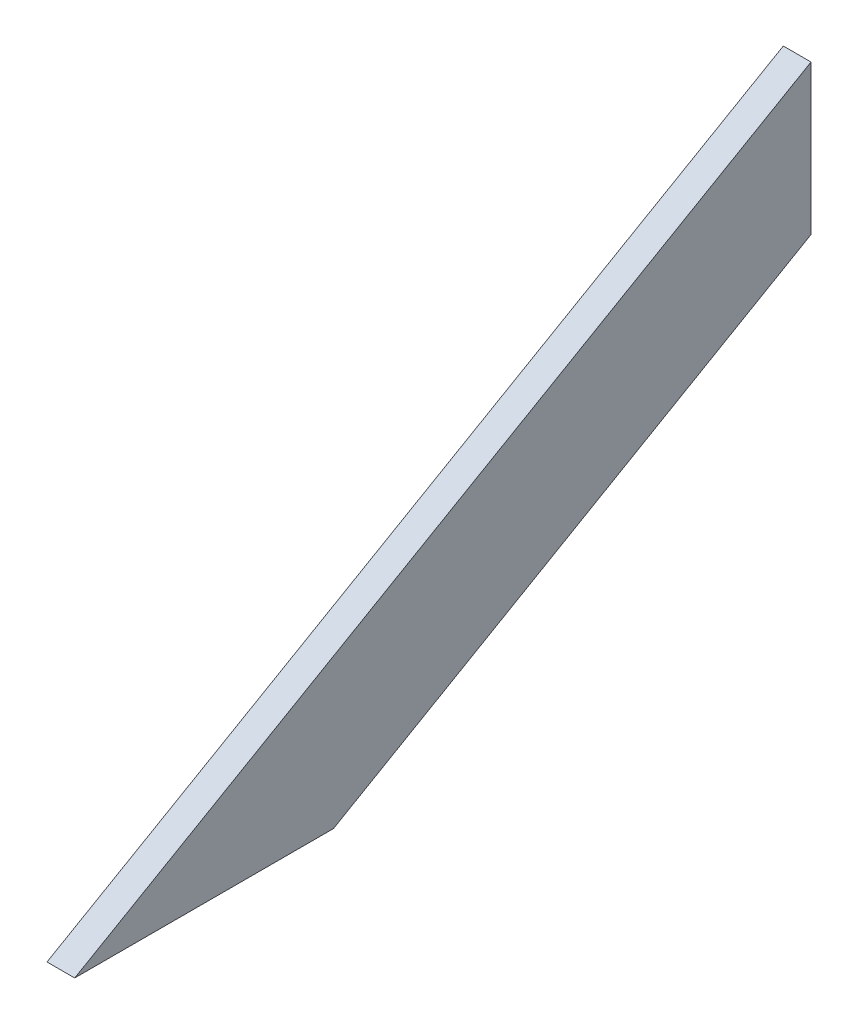
SolidWorks part; units mm, degrees
material "Pine"
ref_plane "Front Plane" through (0, 0, 0) normal (0, 0, 1) x (1, 0, 0)
ref_plane "Top Plane" through (0, 0, 0) normal (0, 1, 0) x (1, 0, 0)
ref_plane "Right Plane" through (0, 0, 0) normal (1, 0, 0) x (0, 0, -1)
sketch "Sketch1" plane through (0, 0, 0) normal (1, 0, 0) x (0, 0, -1)
  line L0 (0, 0) -> (177.8, 0)
  line L1 (177.8, 0) -> (505.932, 189.4471)
  line L2 (505.932, 189.4471) -> (505.932, 292.1)
  line L3 (505.932, 292.1) -> (0, 0)
  point P3 (182.464, 0)
  point P6 (284.0224, 108.5539)
  point P7 (440.3294, 183.6115)
  point P8 (406.2665, 166.889)
  point P9 (385.8237, 94.312)
  dimension "D1" = 30
  dimension "D2" = 584.2
  dimension "D3" = 88.9
extrude "Boss-Extrude1" add sketch "Sketch1" along normal blind 19.05
equation "\"D2@Sketch1\"=2ft-.5in/tan(30)-.5in/tan(75)"
equation "\"D3@Sketch1\"=3.50in"
